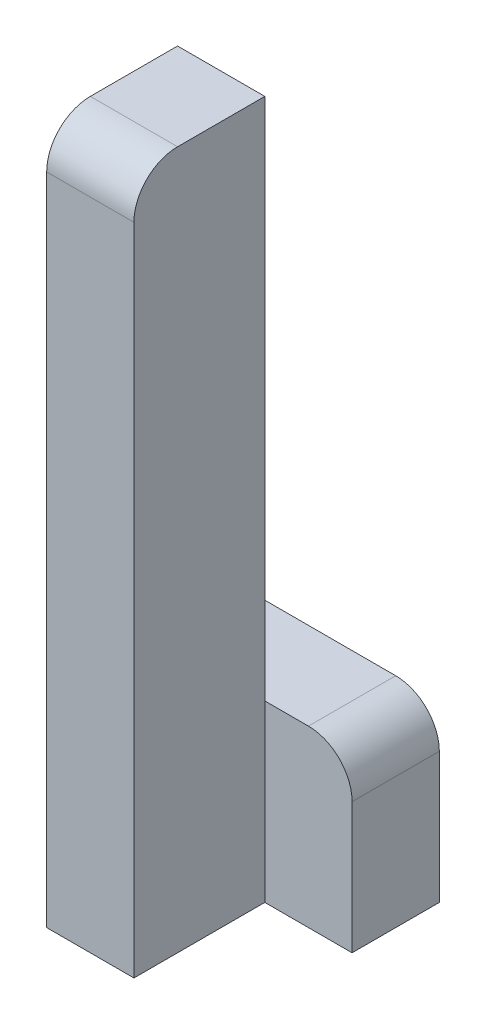
SolidWorks part; units mm, degrees
ref_plane "Front Plane" through (0, 0, 0) normal (0, 0, 1) x (1, 0, 0)
ref_plane "Top Plane" through (0, 0, 0) normal (0, 1, 0) x (1, 0, 0)
ref_plane "Right Plane" through (0, 0, 0) normal (1, 0, 0) x (0, 0, -1)
sketch "Sketch1" plane through (0, 0, 0) normal (0, 0, 1) x (1, 0, 0)
  line L1 (-30, -160) -> (-10, -160)
  line L2 (-10, -160) -> (-10, 0)
  line L3 (-10, 0) -> (-30, 0)
  line L4 (-30, 0) -> (-30, -160)
  dimension "D1" = 20
  dimension "Width" = 160
extrude "Boss-Extrude1" add sketch "Sketch1" along normal blind 30
sketch "Sketch2" plane through (0, 0, 0) normal (0, 0, 1) x (1, 0, 0)
  line L1 (-30, -160) -> (10, -160)
  line L2 (10, -160) -> (10, -120)
  line L3 (10, -120) -> (-30, -120)
  line L4 (-30, -120) -> (-30, -160)
  dimension "D1" = 40
  dimension "Width" = 40
extrude "Boss-Extrude2" add sketch "Sketch2" against normal blind 20
fillet "Fillet1" radius 10 2 edges at (10, -120, -10) (-20, 0, 30)
